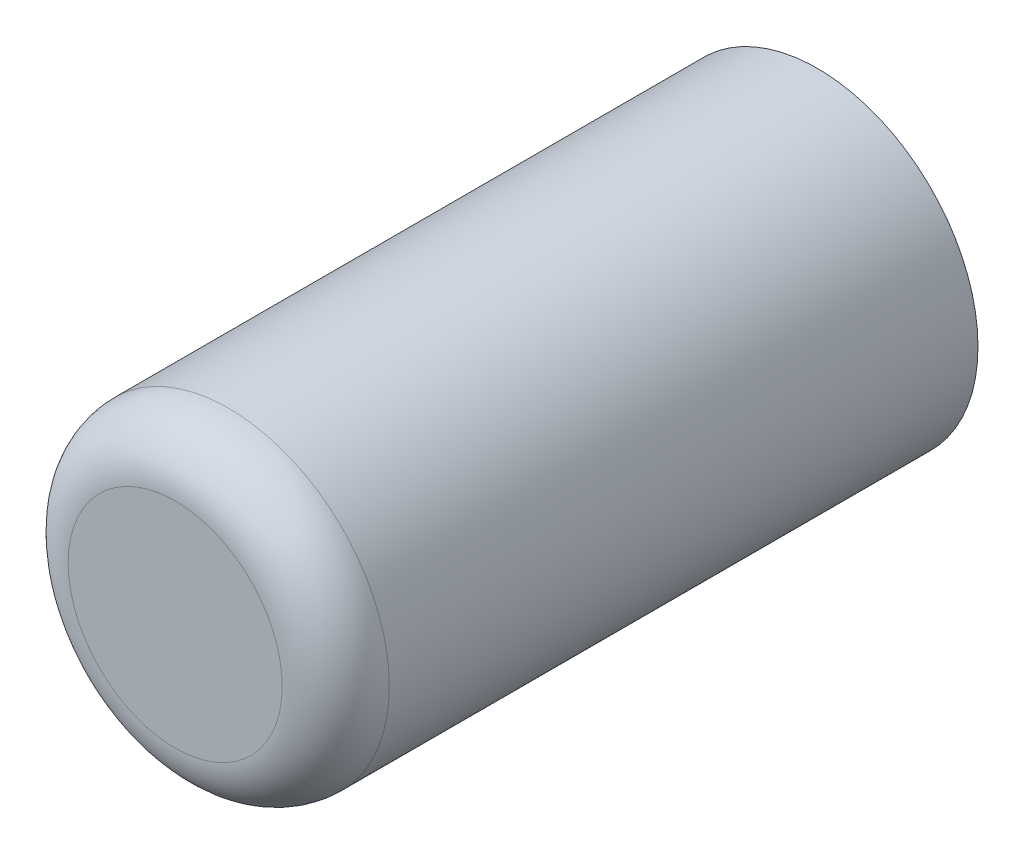
SolidWorks part; units mm, degrees
ref_plane "Přední rovina" through (0, 0, 0) normal (0, 0, 1) x (1, 0, 0)
ref_plane "Vrchní rovina" through (0, 0, 0) normal (0, 1, 0) x (1, 0, 0)
ref_plane "Pravá rovina" through (0, 0, 0) normal (1, 0, 0) x (0, 0, -1)
sketch "Skica2" plane through (0, 0, 0) normal (0, 0, 1) x (1, 0, 0)
  circle A0 centre (0, 0) radius 3
  dimension "D1" = 6
extrude "Přidat vysunutím1" add sketch "Skica2" along normal blind 12
fillet "Zaoblit1" radius 1 1 edges at (3, 0, 12)
